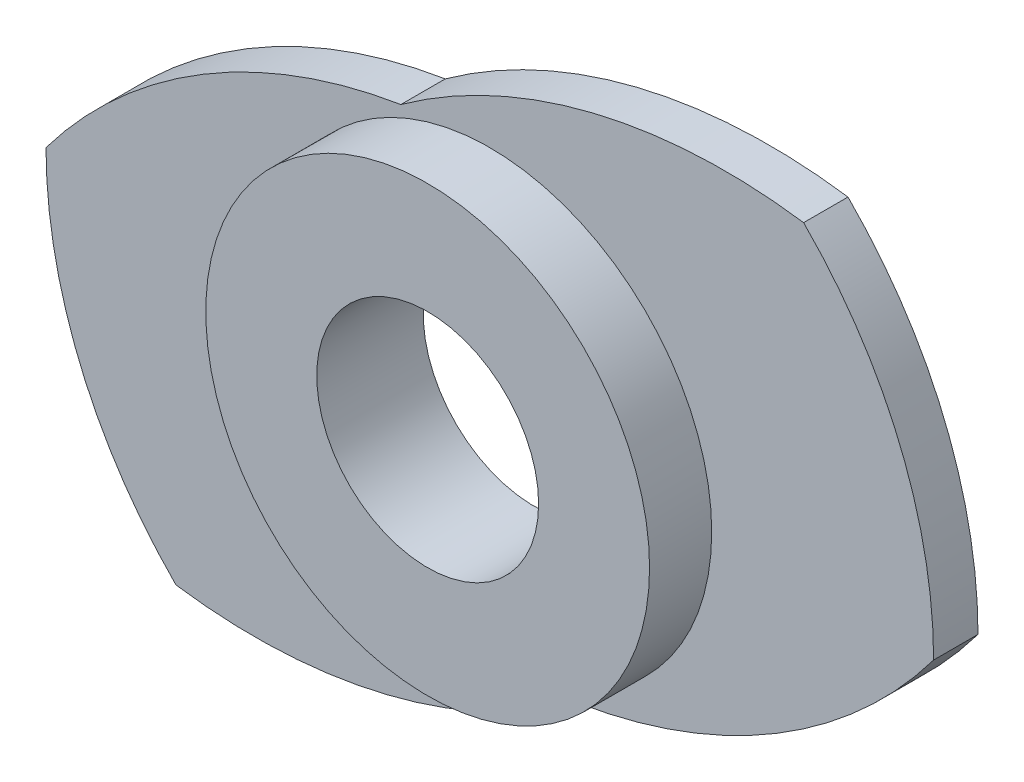
SolidWorks part; units mm, degrees
ref_plane "Front Plane" through (0, 0, 0) normal (0, 0, 1) x (1, 0, 0)
ref_plane "Top Plane" through (0, 0, 0) normal (0, 1, 0) x (1, 0, 0)
ref_plane "Right Plane" through (0, 0, 0) normal (1, 0, 0) x (0, 0, -1)
sketch "Sketch1" plane through (0, 0, 0) normal (0, 0, 1) x (1, 0, 0)
  line L0 (-9.2388, -3.8268) -> (0, 0) construction
  line L1 (0, 0) -> (-3.8268, 9.2388) construction
  line L2 (-3.8268, 9.2388) -> (3.8268, -9.2388) construction
  circle A0 centre (0, 0) radius 10 construction
  circle A1 centre (0, 0) radius 5 construction
  arc A2 (-10, 0) -> (-7.0711, -7.0711) centre (0, 0) ccw
  arc A3 (0, 5) -> (3.5355, -3.5355) centre (0, 0) cw
  arc A4 (3.5355, -3.5355) -> (-7.0711, -7.0711) centre (-5.3033, 5.3033) cw
  arc A5 (0, 5) -> (-10, 0) centre (0, -7.5) ccw
  arc A6 (-3.5355, 3.5355) -> (7.0711, 7.0711) centre (5.3033, -5.3033) cw
  arc A7 (7.0711, 7.0711) -> (10, 0) centre (0, 0) cw
  arc A8 (0, -5) -> (10, 0) centre (0, 7.5) ccw
  point P19 (0, 0)
  dimension "D1" = 20
  dimension "D2" = 5
  dimension "D4" = 12.5
  dimension "D3" = 9.2388
extrude "Boss-Extrude1" add sketch "Sketch1" along normal blind 1
sketch "Sketch2" plane through (0, 0, 1) normal (0, 0, 1) x (1, 0, 0)
  circle A0 centre (0, 0) radius 5
  dimension "D1" = 10
extrude "Boss-Extrude2" add sketch "Sketch2" along normal blind 1.4
sketch "Sketch3" plane through (0, 0, 2.4) normal (0, 0, 1) x (1, 0, 0)
  circle A0 centre (0, 0) radius 2.5
  dimension "D1" = 5
extrude "Cut-Extrude1" cut sketch "Sketch3" against normal blind 8
